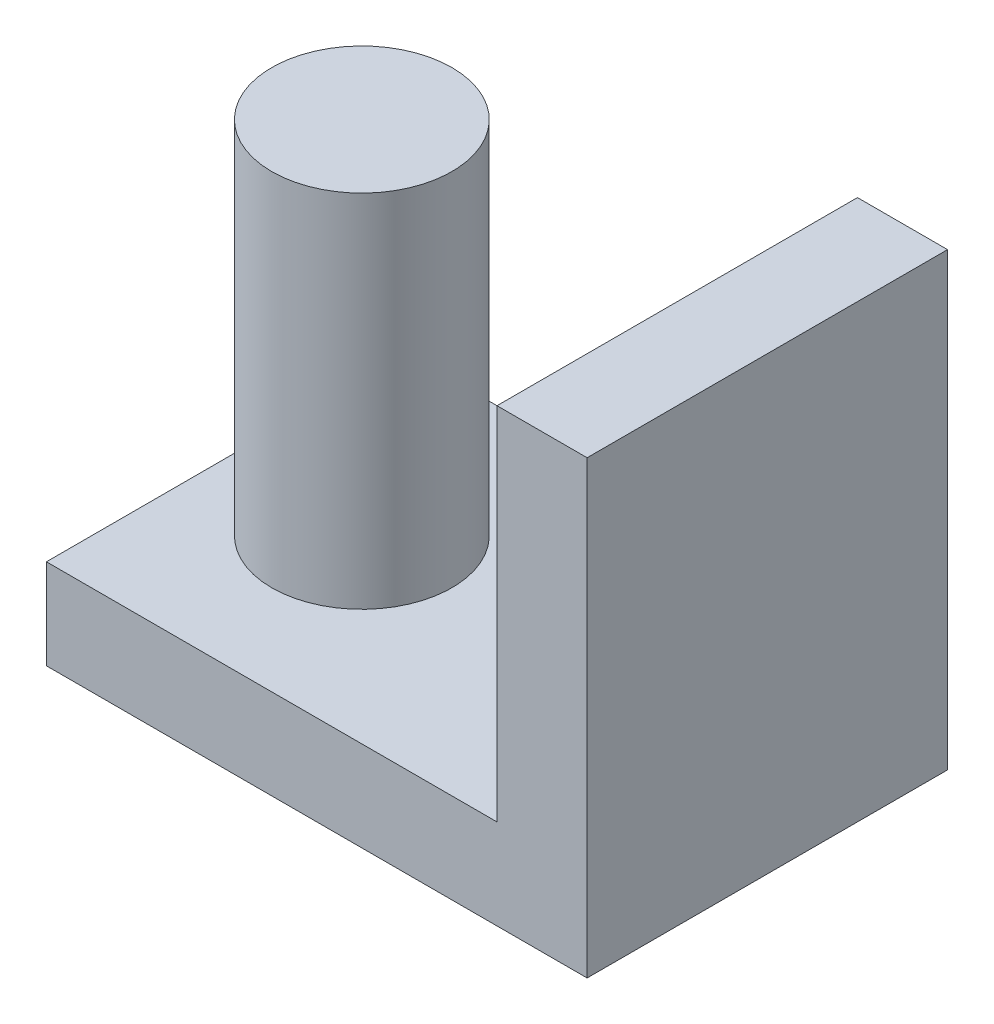
SolidWorks part; units mm, degrees
ref_plane "Front Plane" through (0, 0, 0) normal (0, 0, 1) x (1, 0, 0)
ref_plane "Top Plane" through (0, 0, 0) normal (0, 1, 0) x (1, 0, 0)
ref_plane "Right Plane" through (0, 0, 0) normal (1, 0, 0) x (0, 0, -1)
sketch "Sketch1" plane through (0, 0, 0) normal (0, 1, 0) x (1, 0, 0)
  line L1 (-4.7625, 3.175) -> (4.7625, 3.175)
  line L2 (-4.7625, 3.175) -> (-4.7625, -3.175)
  line L3 (-4.7625, -3.175) -> (4.7625, -3.175)
  line L4 (4.7625, 3.175) -> (4.7625, -3.175)
  line L5 (-4.7625, 3.175) -> (4.7625, -3.175) construction
  line L6 (-4.7625, -3.175) -> (4.7625, 3.175) construction
  point P0 (0, 0)
  dimension "D1" = 6.35
  dimension "D2" = 9.525
extrude "Boss-Extrude1" add sketch "Sketch1" along normal blind 1.5875
sketch "Sketch2" plane through (0, 1.5875, 0) normal (0, 1, 0) x (1, 0, 0)
  line L0 (-4.7625, -3.175) -> (4.7625, -3.175) construction
  line L1 (4.7625, 3.175) -> (3.175, 3.175)
  line L2 (4.7625, 3.175) -> (4.7625, -3.175)
  line L3 (4.7625, -3.175) -> (3.175, -3.175)
  line L4 (3.175, 3.175) -> (3.175, -3.175)
  circle A0 centre (-2.3813, 0) radius 1.5875
  point P9 (0, 0)
  dimension "D1" = 3.175
  dimension "D2" = 1.5875
  dimension "D3" = 2.3813
extrude "Boss-Extrude2" add sketch "Sketch2" along normal blind 6.35
